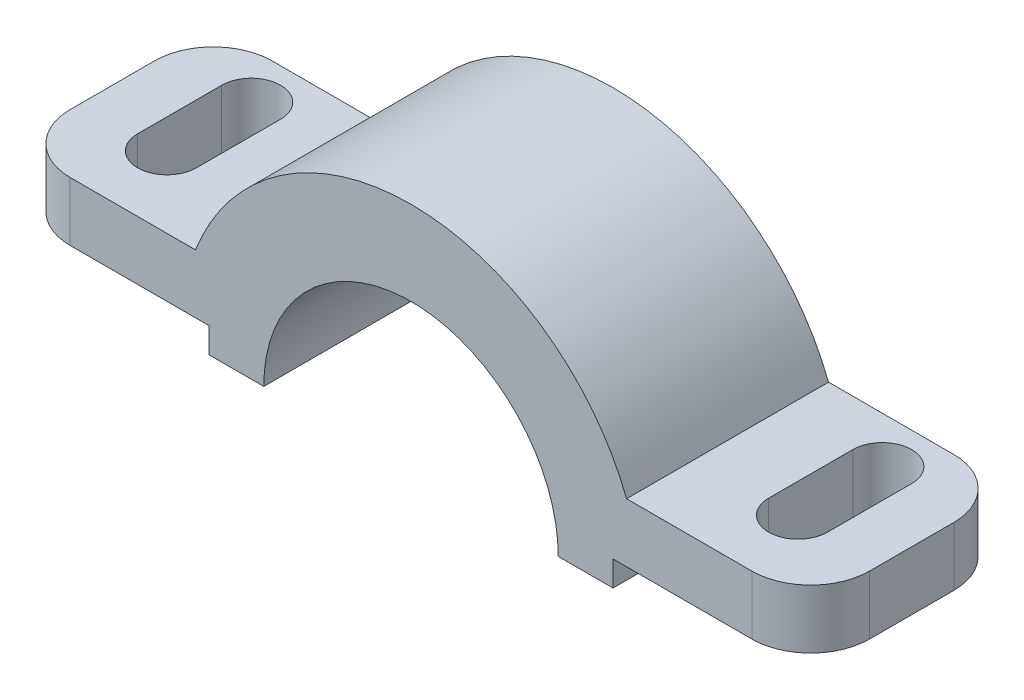
SolidWorks part; units mm, degrees
material "Alloy Steel"
ref_plane "Front Plane" through (0, 0, 0) normal (0, 0, 1) x (1, 0, 0)
ref_plane "Top Plane" through (0, 0, 0) normal (0, 1, 0) x (1, 0, 0)
ref_plane "Right Plane" through (0, 0, 0) normal (1, 0, 0) x (0, 0, -1)
sketch "Sketch1" plane through (0, 0, 0) normal (0, 0, 1) x (1, 0, 0)
  line L0 (35, 0) -> (48, 0)
  line L11 (48, 0) -> (48, 6)
  line L12 (48, 6) -> (95, 6)
  line L13 (95, 6) -> (95, 20)
  line L14 (95, 20) -> (51.2348, 20)
  line L15 (0, 2437.824) -> (0, -1290.9641) construction
  line L16 (-95, 20) -> (-51.2348, 20)
  line L17 (-95, 6) -> (-95, 20)
  line L18 (-48, 6) -> (-95, 6)
  line L19 (-48, 0) -> (-48, 6)
  line L20 (-35, 0) -> (-48, 0)
  arc A2 (-51.2348, 20) -> (51.2348, 20) centre (0, 0) cw
  arc A3 (-35, 0) -> (35, 0) centre (0, 0) cw
  dimension "D1" = 55
  dimension "D2" = 35
  dimension "D3" = 48
  dimension "D4" = 6
  dimension "D5" = 20
  dimension "D6" = 95
extrude "Boss-Extrude1" add sketch "Sketch1" along normal mid plane 48
fillet "Fillet1" radius 14 4 edges at (95, 13, -24) (95, 13, 24) (-95, 13, -24) (-95, 13, 24)
sketch "Sketch2" plane through (0, 20, 0) normal (0, 1, 0) x (1, 0, 0)
  line L0 (75, -7) -> (75, 13) construction
  line L1 (68, -7) -> (68, 13)
  line L2 (82, -7) -> (82, 13)
  line L3 (0, -43.5115) -> (0, 47.6727) construction
  line L4 (-75, -7) -> (-75, 13) construction
  line L5 (-68, -7) -> (-68, 13)
  line L6 (-82, -7) -> (-82, 13)
  line L7 (81, -24) -> (51.2348, -24) construction
  arc A0 (68, -7) -> (82, -7) centre (75, -7) ccw
  arc A1 (82, 13) -> (68, 13) centre (75, 13) ccw
  arc A2 (-68, -7) -> (-82, -7) centre (-75, -7) cw
  arc A3 (-82, 13) -> (-68, 13) centre (-75, 13) cw
  point P2 (75, 3)
  point P14 (-75, 3)
  dimension "D1" = 14
  dimension "D2" = 20
  dimension "D3" = 20
  dimension "D4" = 17
extrude "Cut-Extrude1" cut sketch "Sketch2" against normal through all and the other way through all
equation "\"A\"= 190"
equation "\"B\"= 54"
equation "\"C\"= 20"
equation "\"D\"= 55"
equation "\"E\"= 1"
equation "\"D1@Sketch1\"=\"D\""
equation "\"D6@Sketch1\"=\"A\"/2"
equation "\"D5@Sketch1\"=\"C\""
equation "\"D4@Sketch2\"=(\"B\"-20)/2"
